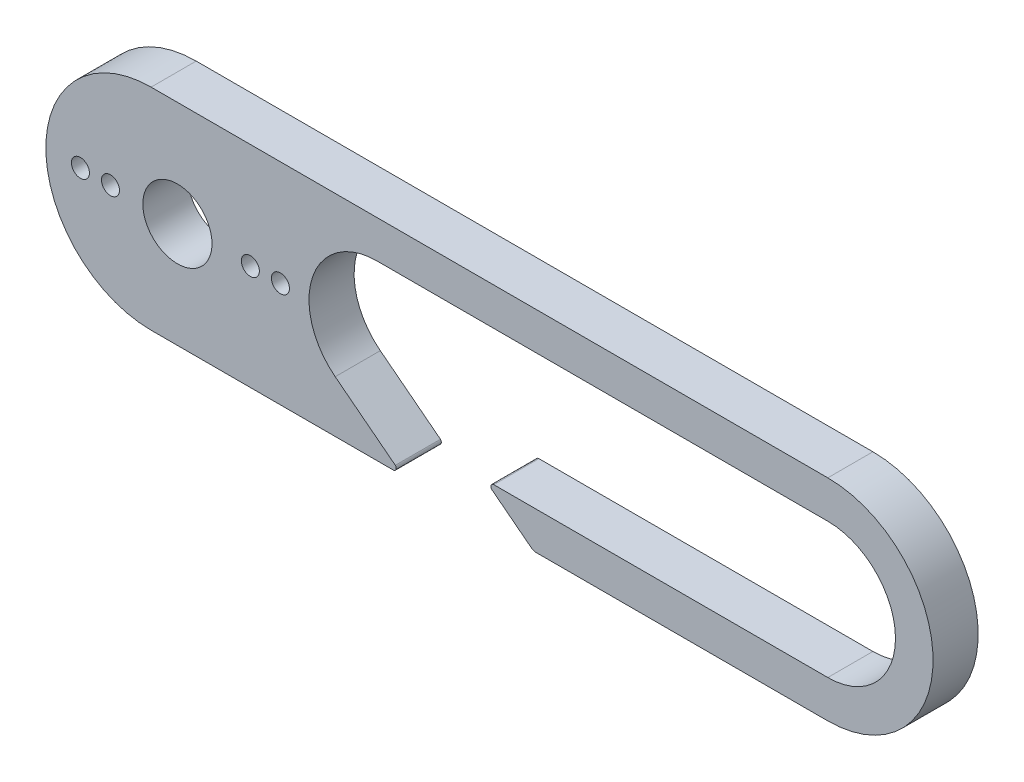
SolidWorks part; units mm, degrees
ref_plane "Front Plane" through (0, 0, 0) normal (0, 0, 1) x (1, 0, 0)
ref_plane "Top Plane" through (0, 0, 0) normal (0, 1, 0) x (1, 0, 0)
ref_plane "Right Plane" through (0, 0, 0) normal (1, 0, 0) x (0, 0, -1)
sketch "Sketch2" plane through (0, 0, 0) normal (0, 0, 1) x (1, 0, 0)
  line L0 (5.2704, 0) -> (54.3236, 0) construction
  line L1 (16.7704, 4.5) -> (46.7704, 4.5)
  line L2 (24.5608, -4.5) -> (46.7704, -4.5)
  line L3 (1.7704, 7) -> (46.7704, 7)
  line L4 (1.7704, -7) -> (17.8716, -7)
  line L5 (1.7704, 4.5) -> (46.7704, 4.5) construction
  line L6 (1.7704, -4.5) -> (46.7704, -4.5) construction
  line L7 (12.2704, 0) -> (46.7704, 0) construction
  line L8 (14.0128, -3.5561) -> (18.0106, -6.6562)
  line L10 (27.0652, -6.8951) -> (24.4383, -4.858)
  line L12 (27.3716, -7) -> (46.7704, -7)
  line L13 (1.7704, -7) -> (46.7704, -7) construction
  line L15 (12.2704, 0) -> (-5.2296, 0) construction
  arc A1 (46.7704, -4.5) -> (46.7704, 4.5) centre (46.7704, 0) ccw
  arc A2 (46.7704, -7) -> (46.7704, 7) centre (46.7704, 0) ccw
  arc A3 (1.7704, 7) -> (1.7704, -7) centre (1.7704, 0) ccw
  circle A4 centre (5.2704, 0) radius 2.5
  arc A6 (16.7704, 4.5) -> (14.0128, -3.5561) centre (16.7704, 0) ccw
  arc A7 (1.7704, 4.5) -> (1.7704, -4.5) centre (1.7704, 0) ccw construction
  arc A8 (24.4383, -4.858) -> (24.5608, -4.5) centre (24.5608, -4.7) cw
  arc A9 (27.3716, -7) -> (27.0652, -6.8951) centre (27.3716, -6.5) cw
  arc A10 (17.8716, -7) -> (18.0106, -6.6562) centre (17.8716, -6.8) ccw
  circle A11 centre (5.2704, 0) radius 2.2653 construction
  arc A12 (5.1037, 2.3451) -> (5.2704, 2.2653) centre (5.2704, 2.479) ccw
  arc A13 (5.1037, 2.3451) -> (4.7384, 2.2901) centre (4.9371, 2.2113) ccw
  arc A14 (4.6027, 2.1646) -> (4.7384, 2.2901) centre (4.5397, 2.3689) ccw
  arc A15 (5.2704, 2.2653) -> (5.437, 2.3451) centre (5.2704, 2.479) ccw
  arc A16 (5.8024, 2.2901) -> (5.437, 2.3451) centre (5.6037, 2.2113) ccw
  arc A17 (5.8024, 2.2901) -> (5.9381, 2.1646) centre (6.0011, 2.3689) ccw
  arc A18 (5.9381, 2.1646) -> (6.1209, 2.1918) centre (6.0011, 2.3689) ccw
  arc A19 (6.4537, 2.0315) -> (6.1209, 2.1918) centre (6.2406, 2.0148) ccw
  arc A20 (6.4537, 2.0315) -> (6.5464, 1.8716) centre (6.6669, 2.0483) ccw
  arc A21 (6.5464, 1.8716) -> (6.7291, 1.8438) centre (6.6669, 2.0483) ccw
  arc A22 (7, 1.5925) -> (6.7291, 1.8438) centre (6.7914, 1.6393) ccw
  arc A23 (7, 1.5925) -> (7.0414, 1.4124) centre (7.2086, 1.5456) ccw
  arc A24 (7.0414, 1.4124) -> (7.2078, 1.3319) centre (7.2086, 1.5456) ccw
  arc A25 (7.3925, 1.0119) -> (7.2078, 1.3319) centre (7.207, 1.1181) ccw
  arc A26 (7.3925, 1.0119) -> (7.379, 0.8276) centre (7.578, 0.9057) ccw
  arc A27 (7.379, 0.8276) -> (7.5143, 0.7016) centre (7.578, 0.9057) ccw
  arc A28 (7.5965, 0.3414) -> (7.5143, 0.7016) centre (7.4505, 0.4976) ccw
  arc A29 (7.5965, 0.3414) -> (7.5293, 0.1693) centre (7.7425, 0.1853) ccw
  arc A30 (7.5293, 0.1693) -> (7.6214, 0.0091) centre (7.7425, 0.1853) ccw
  arc A31 (7.5938, -0.3594) -> (7.6214, 0.0091) centre (7.5004, -0.1671) ccw
  arc A32 (7.5938, -0.3594) -> (7.4788, -0.5041) centre (7.6872, -0.5516) ccw
  arc A33 (7.4788, -0.5041) -> (7.5196, -0.6843) centre (7.6872, -0.5516) ccw
  arc A34 (7.3846, -1.0283) -> (7.5196, -0.6843) centre (7.352, -0.817) ccw
  arc A35 (7.3846, -1.0283) -> (7.2321, -1.1326) centre (7.4173, -1.2395) ccw
  arc A36 (7.2321, -1.1326) -> (7.218, -1.3169) centre (7.4173, -1.2395) ccw
  arc A37 (6.9876, -1.6058) -> (7.218, -1.3169) centre (7.0187, -1.3943) ccw
  arc A38 (6.9876, -1.6058) -> (6.8111, -1.6606) centre (6.9565, -1.8173) ccw
  arc A39 (6.8111, -1.6606) -> (6.7433, -1.8325) centre (6.9565, -1.8173) ccw
  arc A40 (6.438, -2.0406) -> (6.7433, -1.8325) centre (6.5301, -1.8477) ccw
  arc A41 (6.438, -2.0406) -> (6.2532, -2.0409) centre (6.346, -2.2335) ccw
  arc A42 (6.2532, -2.0409) -> (6.1377, -2.1852) centre (6.346, -2.2335) ccw
  arc A43 (5.7847, -2.2941) -> (6.1377, -2.1852) centre (5.9295, -2.1369) ccw
  arc A44 (5.7847, -2.2941) -> (5.608, -2.24) centre (5.6398, -2.4513) ccw
  arc A45 (5.608, -2.24) -> (5.4551, -2.3438) centre (5.6398, -2.4513) ccw
  arc A46 (5.0856, -2.3438) -> (5.4551, -2.3438) centre (5.2704, -2.2362) ccw
  arc A47 (5.0856, -2.3438) -> (4.9328, -2.24) centre (4.9009, -2.4513) ccw
  arc A48 (4.9328, -2.24) -> (4.7561, -2.2941) centre (4.9009, -2.4513) ccw
  arc A49 (4.403, -2.1852) -> (4.7561, -2.2941) centre (4.6112, -2.1369) ccw
  arc A50 (4.403, -2.1852) -> (4.2875, -2.0409) centre (4.1948, -2.2335) ccw
  arc A51 (4.2875, -2.0409) -> (4.1027, -2.0406) centre (4.1948, -2.2335) ccw
  arc A52 (3.7974, -1.8325) -> (4.1027, -2.0406) centre (4.0107, -1.8477) ccw
  arc A53 (3.7974, -1.8325) -> (3.7296, -1.6606) centre (3.5842, -1.8173) ccw
  arc A54 (3.7296, -1.6606) -> (3.5531, -1.6058) centre (3.5842, -1.8173) ccw
  arc A55 (3.3227, -1.3169) -> (3.5531, -1.6058) centre (3.522, -1.3943) ccw
  arc A56 (3.3227, -1.3169) -> (3.3086, -1.1326) centre (3.1235, -1.2395) ccw
  arc A57 (3.3086, -1.1326) -> (3.1561, -1.0283) centre (3.1235, -1.2395) ccw
  arc A58 (3.0211, -0.6843) -> (3.1561, -1.0283) centre (3.1887, -0.817) ccw
  arc A59 (3.0211, -0.6843) -> (3.0619, -0.5041) centre (2.8535, -0.5516) ccw
  arc A60 (3.0619, -0.5041) -> (2.9469, -0.3594) centre (2.8535, -0.5516) ccw
  arc A61 (2.9193, 0.0091) -> (2.9469, -0.3594) centre (3.0404, -0.1671) ccw
  arc A62 (2.9193, 0.0091) -> (3.0114, 0.1693) centre (2.7983, 0.1853) ccw
  arc A63 (3.0114, 0.1693) -> (2.9442, 0.3414) centre (2.7983, 0.1853) ccw
  arc A64 (3.0265, 0.7016) -> (2.9442, 0.3414) centre (3.0902, 0.4976) ccw
  arc A65 (3.0265, 0.7016) -> (3.1617, 0.8276) centre (2.9627, 0.9057) ccw
  arc A66 (3.1617, 0.8276) -> (3.1482, 1.0119) centre (2.9627, 0.9057) ccw
  arc A67 (3.333, 1.3319) -> (3.1482, 1.0119) centre (3.3337, 1.1181) ccw
  arc A68 (3.333, 1.3319) -> (3.4993, 1.4124) centre (3.3322, 1.5456) ccw
  arc A69 (3.4993, 1.4124) -> (3.5408, 1.5925) centre (3.3322, 1.5456) ccw
  arc A70 (3.8116, 1.8438) -> (3.5408, 1.5925) centre (3.7493, 1.6393) ccw
  arc A71 (3.8116, 1.8438) -> (3.9943, 1.8716) centre (3.8739, 2.0483) ccw
  arc A72 (3.9943, 1.8716) -> (4.087, 2.0315) centre (3.8739, 2.0483) ccw
  arc A73 (4.4199, 2.1918) -> (4.087, 2.0315) centre (4.3001, 2.0148) ccw
  arc A74 (4.4199, 2.1918) -> (4.6027, 2.1646) centre (4.5397, 2.3689) ccw
  circle A75 centre (3.5204, 0) radius 1.05
  circle A76 centre (3.5204, 0) radius 2.3
  circle A77 centre (8.3704, 0) radius 0.6
  circle A78 centre (10.3704, 0) radius 0.6
  circle A79 centre (12.3704, 0) radius 0.6
  circle A80 centre (-0.9296, 0) radius 0.6
  circle A81 centre (-2.9296, 0) radius 0.6
  circle A82 centre (-4.9296, 0) radius 0.6
  point P3 (25, 0)
  point P32 (5.2704, 0)
  point P34 (5.2704, 0)
  point P159 (5.2704, 0)
  point P176 (3.5204, 0)
  dimension "D2" = 30
  dimension "D3" = 45
  dimension "D5" = 5
  dimension "D6" = 4.5
  dimension "D7" = 4.5
  dimension "D8" = 0.2
  dimension "D9" = 0.5
  dimension "D10" = 0.2
  dimension "D1" = 2.5
  dimension "D4" = 3.5
  dimension "D11" = 9.5
  dimension "D12" = 2.2362
  dimension "D13" = 2
  dimension "D14" = 2
  dimension "D15" = 2
  dimension "D16" = 2
  dimension "D17" = 4.45
  dimension "D18" = 4.85
extrude "Boss-Extrude1" add sketch "Sketch2" along normal blind 3 contours A82 A3 L4 A10 L8 A6 A79 L1 A1 L2 A8 L10 A9 L12 A2 L3 A81 A80 A78 A77 A4 A76 | A6 A79 | A3 A82 | A77 A28 A27 A26 A25 A24 A23 A22 A21 A20 A19 A18 A17 A16 A15 A12 A13 A14 A74 A73 A76 A52 A51 A50 A49 A48 A47 A46 A45 A44 A43 A42 A41 A40 A39 A38 A37 A36 A35 A34 A33 A32 | A76 A73 A74 A14 A13 A12 A15 A16 A17 A18 A19 A20 A21 A22 A23 A24 A25 A26 A27 A28 A29 A30 A31 A32 A33 A34 A35 A36 A37 A38 A39 A40 A41 A42 A43 A44 A45 A46 A47 A48 A49 A50 A4 | A75
